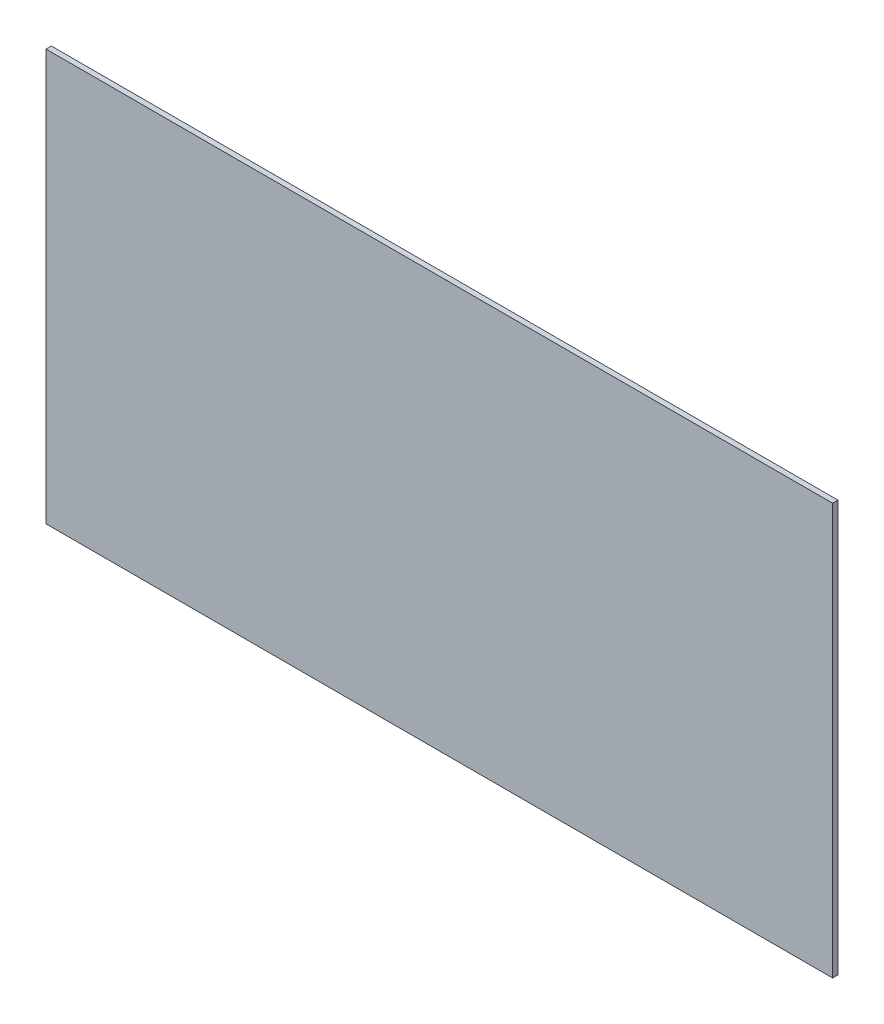
SolidWorks part; units mm, degrees
ref_plane "Alzado" through (0, 0, 0) normal (0, 0, 1) x (1, 0, 0)
ref_plane "Planta" through (0, 0, 0) normal (0, 1, 0) x (1, 0, 0)
ref_plane "Vista lateral" through (0, 0, 0) normal (1, 0, 0) x (0, 0, -1)
sketch "Croquis1" plane through (0, 0, 0) normal (0, 0, 1) x (1, 0, 0)
  line L0 (0, 0) -> (10941.1588, 0) construction
  line L1 (0, 0) -> (0, 10941.1588) construction
  line L3 (-220, 115) -> (220, 115)
  line L4 (-220, 115) -> (-220, -115)
  line L5 (-220, -115) -> (220, -115)
  line L6 (220, 115) -> (220, -115)
  line L7 (-220, 115) -> (220, -115) construction
  line L8 (-220, -115) -> (220, 115) construction
  point P5 (0, 0)
  dimension "D1" = 440
  dimension "D2" = 230
extrude "Saliente-Extruir1" add sketch "Croquis1" along normal blind 3
